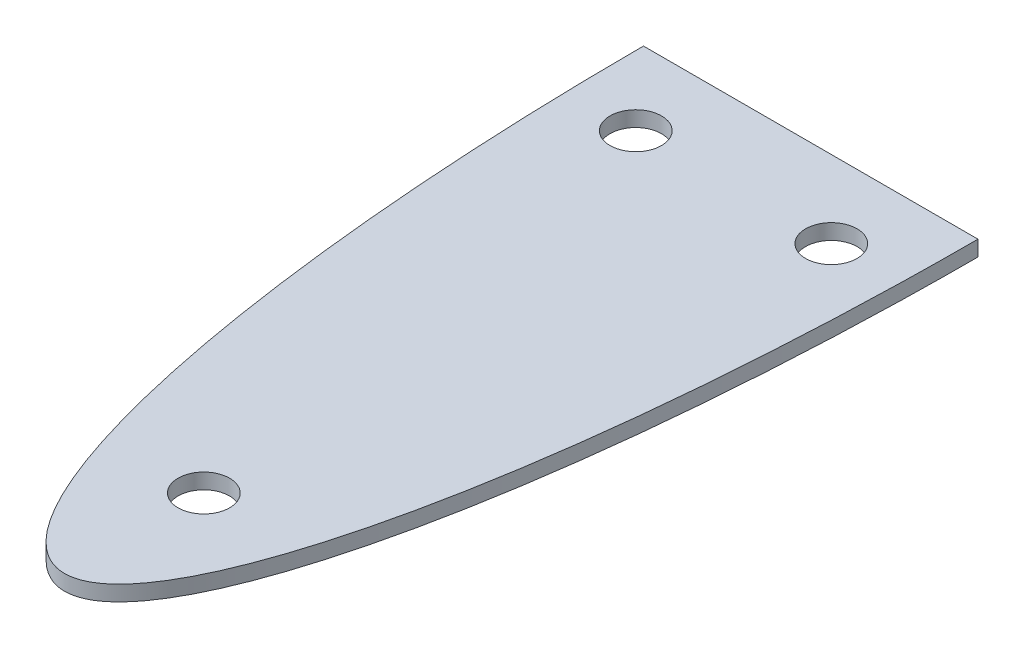
SolidWorks part; units mm, degrees
ref_plane "Front Plane" through (0, 0, 0) normal (0, 0, 1) x (1, 0, 0)
ref_plane "Top Plane" through (0, 0, 0) normal (0, 1, 0) x (1, 0, 0)
ref_plane "Right Plane" through (0, 0, 0) normal (1, 0, 0) x (0, 0, -1)
sketch "Sketch2" plane through (0, 0, 0) normal (0, 1, 0) x (1, 0, 0)
  line L0 (-32.5, 0) -> (32.5, 0)
  ellipse E0 centre (0, 0) end of major axis (0, 145) minor radius 32.5 (-32.5, 0) -> (32.5, 0) ccw
  point P4 (0, 0)
  dimension "D1" = 65
  dimension "D2" = 145
extrude "Boss-Extrude1" add sketch "Sketch2" along normal blind 3
sketch "Sketch3" plane through (0, 3, 0) normal (0, 1, 0) x (1, 0, 0)
  line L0 (0, 0) -> (0, -145) construction
  line L1 (32.5, 0) -> (-32.5, 0) construction
  circle A0 centre (-19, -15) radius 5
  circle A1 centre (0, -117.9248) radius 5
  circle A3 centre (19, -15) radius 5
  ellipse E0 centre (0, 0) end of major axis (0, 145) minor radius 32.5 (-32.5, 0) -> (32.5, 0) ccw construction
  point P15 (0, -117.9248)
  dimension "D1" = 10
  dimension "D2" = 10
  dimension "D3" = 19
  dimension "D4" = 15
extrude "Cut-Extrude1" cut sketch "Sketch3" against normal through all
